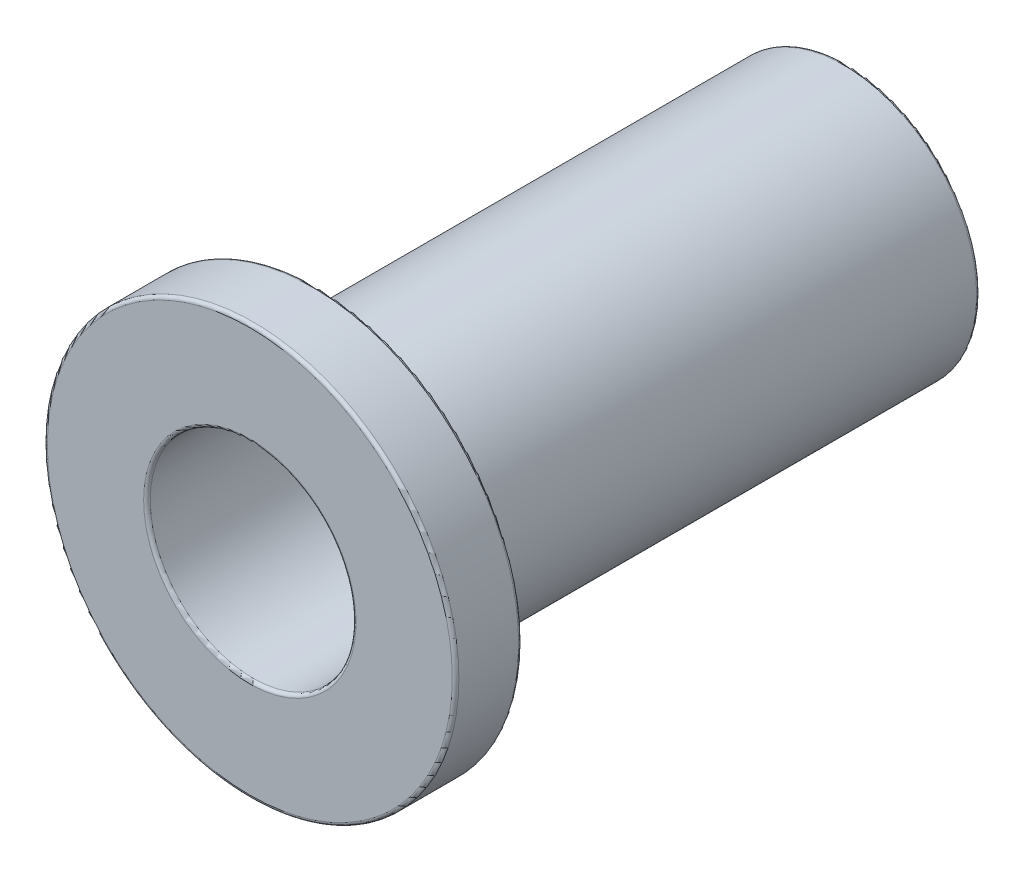
SolidWorks part; units mm, degrees
ref_plane "Front Plane" through (0, 0, 0) normal (0, 0, 1) x (1, 0, 0)
ref_plane "Top Plane" through (0, 0, 0) normal (0, 1, 0) x (1, 0, 0)
ref_plane "Right Plane" through (0, 0, 0) normal (1, 0, 0) x (0, 0, -1)
sketch "Sketch1" plane through (0, 0, 0) normal (-1, 0, 0) x (0, 0, 1)
  line L0 (4.5, 1.55) -> (-4.5, 1.55)
  line L1 (-4.5, 1.55) -> (-4.5, 2)
  line L2 (-4.5, 2) -> (3.5, 2)
  line L3 (3.5, 2) -> (3.5, 3.1)
  line L4 (3.5, 3.1) -> (4.5, 3.1)
  line L6 (4.5, 3.1) -> (4.5, 1.55)
  line L7 (4.5, 0) -> (-4.5, 0) construction
  dimension "ID" = 3.1
  dimension "OD" = 6.2
  dimension "Sleeve OD" = 4
  dimension "Thickness" = 1
  dimension "Overall Height" = 9
sketch "Sketch2" plane through (0, 0, 0) normal (1, 0, 0) x (0, 0, -1)
  line L6 (-4.5, 1.55) -> (4.5, 1.55)
  line L7 (4.5, 1.55) -> (4.5, 2)
  line L8 (4.5, 2) -> (-3.5, 2)
  line L9 (-3.5, 2) -> (-3.5, 3.1)
  line L10 (-3.5, 3.1) -> (-4.5, 3.1)
  line L11 (-4.5, 3.1) -> (-4.5, 1.55)
  line L12 (-4.5, 1.55) -> (4.5, 1.55)
  line L13 (4.5, 1.55) -> (4.5, 2)
  line L14 (4.5, 2) -> (-3.5, 2)
  line L15 (-3.5, 2) -> (-3.5, 3.1)
  line L16 (-3.5, 3.1) -> (-4.5, 3.1)
  line L17 (-4.5, 3.1) -> (-4.5, 1.55)
  dimension "D1" = 0
revolve "Revolve1" add sketch "Sketch2" angle 360 about L7
fillet "Fillet1" radius 0.05 6 edges at (1.55, 0, 4.5) (1.55, 0, -4.5) (2, 0, -4.5) (2, 0, 3.5) (3.1, 0, 3.5) (3.1, 0, 4.5)
equation "\"D1@Fillet1\"=\"Thickness@Sketch1\"*0.05"
